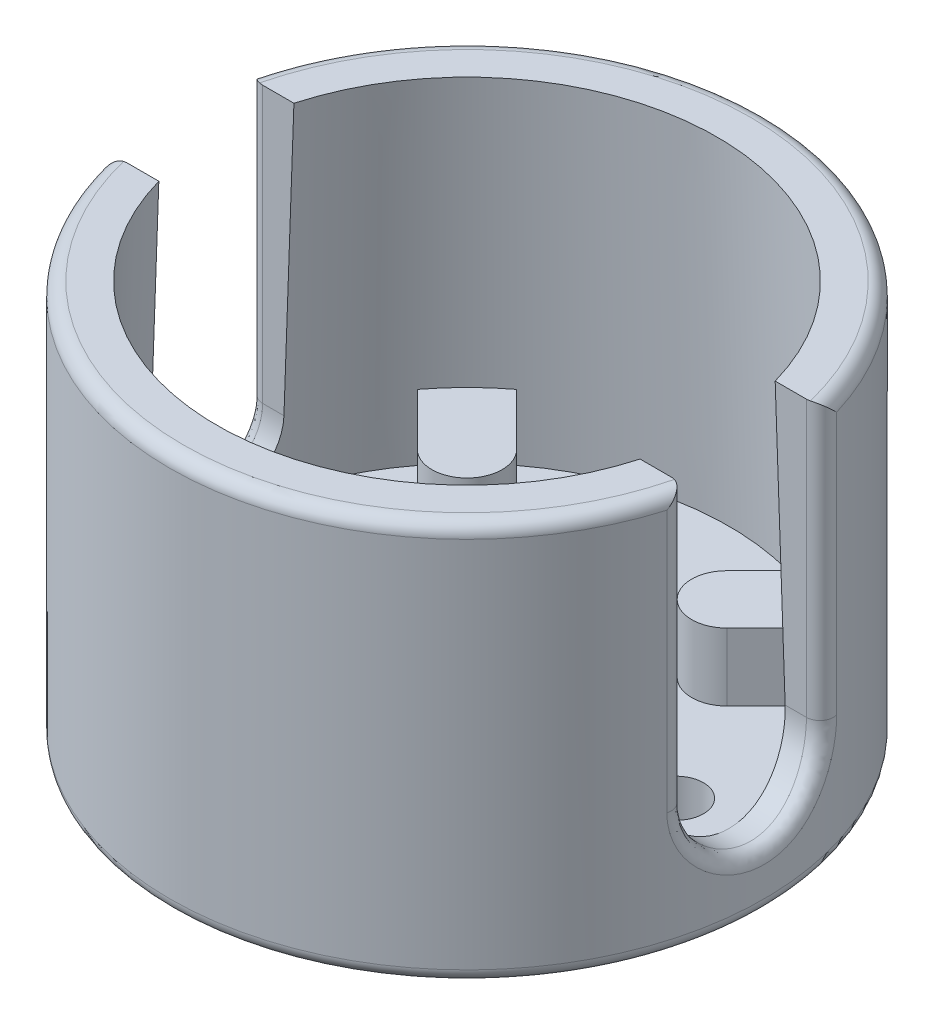
SolidWorks part; units mm, degrees
material "ABS"
ref_plane "Front Plane" through (0, 0, 0) normal (0, 0, 1) x (1, 0, 0)
ref_plane "Top Plane" through (0, 0, 0) normal (0, 1, 0) x (1, 0, 0)
ref_plane "Right Plane" through (0, 0, 0) normal (1, 0, 0) x (0, 0, -1)
sketch "Sketch1" plane through (0, 0, 0) normal (0, 1, 0) x (1, 0, 0)
  circle A0 centre (0, 0) radius 11
  dimension "D1" = 22
extrude "Boss-Extrude1" add sketch "Sketch1" along normal blind 14.8
sketch "Sketch2" plane through (0, 14.8, 0) normal (0, 1, 0) x (1, 0, 0)
  circle A0 centre (0, 0) radius 9.25
  dimension "D1" = 18.5
extrude "Cut-Extrude1" cut sketch "Sketch2" against normal blind 12.7 draft 2 draft outward yes
sketch "Sketch3" plane through (0, 2.1, 0) normal (0, 1, 0) x (1, 0, 0)
  circle A0 centre (0, 0) radius 5.5
  dimension "D1" = 11
extrude "Cut-Extrude2" cut sketch "Sketch3" against normal up to next
sketch "Sketch4" plane through (0, 2.1, 0) normal (0, 1, 0) x (1, 0, 0)
  line L0 (0, 0) -> (-35355.3391, -35355.3391) construction
  line L1 (3.8891, 5.7276) -> (5.8732, 7.7117)
  line L2 (0, 0) -> (0, 50000) construction
  line L3 (5.7276, 3.8891) -> (7.7117, 5.8732)
  line L4 (3.8891, -5.7276) -> (5.8732, -7.7117)
  line L5 (5.7276, -3.8891) -> (7.7117, -5.8732)
  line L6 (-5.7276, -3.8891) -> (-7.7117, -5.8732)
  line L7 (-3.8891, -5.7276) -> (-5.8732, -7.7117)
  line L8 (-3.8891, 5.7276) -> (-5.8732, 7.7117)
  line L9 (-5.7276, 3.8891) -> (-7.7117, 5.8732)
  arc A0 (3.8891, 5.7276) -> (5.7276, 3.8891) centre (4.8083, 4.8083) ccw
  circle A1 centre (0, 0) radius 5.5 construction
  circle A2 centre (0, 0) radius 9.6935 construction
  arc A3 (7.7117, 5.8732) -> (5.8732, 7.7117) centre (0, 0) ccw
  arc A4 (5.8732, -7.7117) -> (7.7117, -5.8732) centre (0, 0) ccw
  arc A5 (5.7276, -3.8891) -> (3.8891, -5.7276) centre (4.8083, -4.8083) ccw
  arc A6 (-7.7117, -5.8732) -> (-5.8732, -7.7117) centre (0, 0) ccw
  arc A7 (-3.8891, -5.7276) -> (-5.7276, -3.8891) centre (-4.8083, -4.8083) ccw
  arc A8 (-5.8732, 7.7117) -> (-7.7117, 5.8732) centre (0, 0) ccw
  arc A9 (-5.7276, 3.8891) -> (-3.8891, 5.7276) centre (-4.8083, 4.8083) ccw
  point P32 (0, 0)
  dimension "D2" = 2.6
  dimension "D1" = 45
  dimension "D3" = 4
extrude "Boss-Extrude2" add sketch "Sketch4" along normal blind 2.5
ref_plane "Plane1" through (-11, 0, 0) normal (-1, 0, 0) x (0, 0, 1)
sketch "Sketch6" plane through (-11, 0, 0) normal (-1, 0, 0) x (0, 0, 1)
  line L1 (5.8732, 2.1) -> (-5.8732, 2.1) construction
  line L2 (-2.5, 4.6) -> (-2.5, 14.8)
  line L3 (9.25, 14.8) -> (-9.25, 14.8) construction
  line L4 (-2.5, 14.8) -> (2.5, 14.8)
  line L5 (11, 14.8) -> (-11, 14.8) construction
  line L6 (2.5, 14.8) -> (2.5, 4.6)
  arc A0 (-2.5, 4.6) -> (2.5, 4.6) centre (0, 4.6) ccw
extrude "Cut-Extrude3" cut sketch "Sketch6" against normal through all
sketch "Sketch7" plane through (0, 0, 0) normal (0, -1, 0) x (1, 0, 0)
  line L0 (0, 0) -> (0, -50000) construction
  circle A0 centre (7.75, 0) radius 1
  circle A1 centre (-7.75, 0) radius 1
  dimension "D1" = 2
  dimension "D2" = 7.75
extrude "Cut-Extrude4" cut sketch "Sketch7" against normal up to next
fillet "Fillet1" radius 0.5 9 edges at (0, 0, 11) (0, 14.8, -11) (10.7121, 9.7, -2.5) (-10.7121, 9.7, -2.5) (10.997, 2.1134, 0.2588) (-10.997, 2.1134, -0.2588) (10.7121, 9.7, 2.5) (-10.7121, 9.7, 2.5) (0, 14.8, 11)
